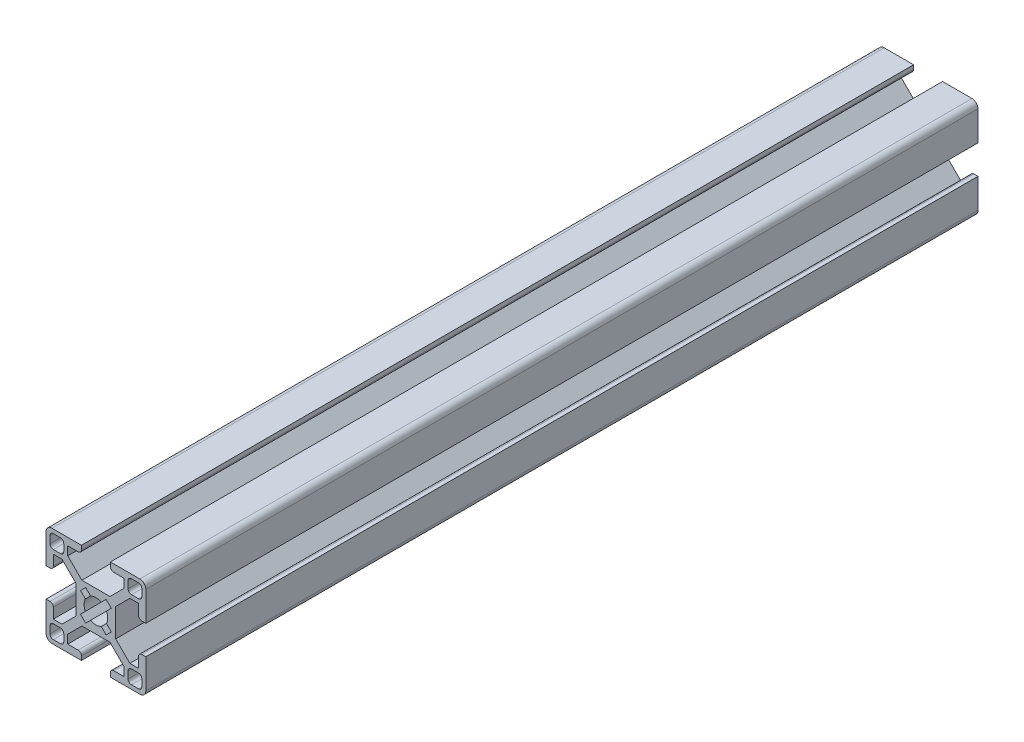
SolidWorks part; units mm, degrees
ref_plane "Front Plane" through (0, 0, 0) normal (0, 0, 1) x (1, 0, 0)
ref_plane "Top Plane" through (0, 0, 0) normal (0, 1, 0) x (1, 0, 0)
ref_plane "Right Plane" through (0, 0, 0) normal (1, 0, 0) x (0, 0, -1)
sketch "Sketch1" plane through (0, 0, 0) normal (0, 0, 1) x (1, 0, 0)
  line L0 (0, 0) -> (5.95, 0) construction
  line L1 (0, 0) -> (0, 5.95) construction
  line L2 (-5.95, 5.95) -> (5.95, 5.95)
  line L3 (5.95, 5.95) -> (5.95, 0)
  line L4 (4.2176, 5.95) -> (8.4602, 10.1926)
  line L5 (5.95, 5.95) -> (8.4425, 8.4425) construction
  line L6 (5.95, 4.2176) -> (10.1926, 8.4602)
  line L7 (8.4602, 12.7926) -> (8.4602, 8.4602)
  line L8 (8.4602, 8.4602) -> (12.7926, 8.4602)
  line L9 (12.7926, 8.4602) -> (12.7926, 5.3502)
  line L10 (13.7926, 4.3502) -> (14.9926, 4.3502)
  line L11 (14.9926, 4.3502) -> (14.9926, 13.1926)
  line L12 (8.4602, 8.4602) -> (14.9926, 14.9926) construction
  line L13 (4.3502, 13.7926) -> (4.3502, 14.9926)
  line L14 (4.3502, 14.9926) -> (13.1926, 14.9926)
  line L15 (5.3502, 12.7926) -> (8.4602, 12.7926)
  line L16 (-9.6602, 9.6602) -> (-13.7926, 13.7926) construction
  line L17 (10.6602, 13.7926) -> (12.7926, 13.7926)
  line L18 (9.6602, 12.7926) -> (9.6602, 10.6602)
  line L19 (10.6602, 9.6602) -> (12.7926, 9.6602)
  line L20 (13.7926, 12.7926) -> (13.7926, 10.6602)
  line L21 (9.6602, 13.7926) -> (13.7926, 9.6602) construction
  line L22 (9.6602, 9.6602) -> (13.7926, 13.7926) construction
  line L23 (-9.6602, 13.7926) -> (-13.7926, 9.6602) construction
  line L24 (-8.4602, 8.4602) -> (-14.9926, 14.9926) construction
  line L25 (-5.95, 5.95) -> (-8.4425, 8.4425) construction
  line L26 (-13.7926, 12.7926) -> (-13.7926, 10.6602)
  line L27 (-10.6602, 9.6602) -> (-12.7926, 9.6602)
  line L28 (-9.6602, 12.7926) -> (-9.6602, 10.6602)
  line L29 (-10.6602, 13.7926) -> (-12.7926, 13.7926)
  line L30 (-5.3502, 12.7926) -> (-8.4602, 12.7926)
  line L31 (-4.3502, 14.9926) -> (-13.1926, 14.9926)
  line L32 (-4.3502, 13.7926) -> (-4.3502, 14.9926)
  line L33 (-14.9926, 4.3502) -> (-14.9926, 13.1926)
  line L34 (-13.7926, 4.3502) -> (-14.9926, 4.3502)
  line L35 (-12.7926, 8.4602) -> (-12.7926, 5.3502)
  line L36 (-8.4602, 8.4602) -> (-12.7926, 8.4602)
  line L37 (-8.4602, 12.7926) -> (-8.4602, 8.4602)
  line L38 (-5.95, 4.2176) -> (-10.1926, 8.4602)
  line L39 (-4.2176, 5.95) -> (-8.4602, 10.1926)
  line L40 (-5.95, 5.95) -> (-5.95, 0)
  line L41 (-5.95, 0) -> (5.95, 0)
  arc A0 (13.1926, 14.9926) -> (14.9926, 13.1926) centre (13.1926, 13.1926) cw
  arc A1 (10.6602, 13.7926) -> (9.6602, 12.7926) centre (10.6602, 12.7926) ccw
  arc A2 (12.7926, 13.7926) -> (13.7926, 12.7926) centre (12.7926, 12.7926) cw
  arc A3 (12.7926, 9.6602) -> (13.7926, 10.6602) centre (12.7926, 10.6602) ccw
  arc A4 (9.6602, 10.6602) -> (10.6602, 9.6602) centre (10.6602, 10.6602) ccw
  arc A5 (4.3502, 13.7926) -> (5.3502, 12.7926) centre (5.3502, 13.7926) ccw
  arc A6 (12.7926, 5.3502) -> (13.7926, 4.3502) centre (13.7926, 5.3502) ccw
  arc A7 (-12.7926, 5.3502) -> (-13.7926, 4.3502) centre (-13.7926, 5.3502) cw
  arc A8 (-4.3502, 13.7926) -> (-5.3502, 12.7926) centre (-5.3502, 13.7926) cw
  arc A9 (-9.6602, 10.6602) -> (-10.6602, 9.6602) centre (-10.6602, 10.6602) cw
  arc A10 (-12.7926, 9.6602) -> (-13.7926, 10.6602) centre (-12.7926, 10.6602) cw
  arc A11 (-12.7926, 13.7926) -> (-13.7926, 12.7926) centre (-12.7926, 12.7926) ccw
  arc A12 (-10.6602, 13.7926) -> (-9.6602, 12.7926) centre (-10.6602, 12.7926) cw
  arc A13 (-13.1926, 14.9926) -> (-14.9926, 13.1926) centre (-13.1926, 13.1926) ccw
  point P12 (11.7264, 11.7264)
  point P40 (4.3502, 12.7926)
  point P43 (12.7926, 4.3502)
  point P82 (-12.7926, 4.3502)
  point P83 (-4.3502, 12.7926)
  point P84 (-11.7264, 11.7264)
  dimension "D9" = 1.8
  dimension "D10" = 1
  dimension "D11" = 1
  dimension "D1" = 5.95
  dimension "D4" = 2.6
  dimension "D2" = 135
  dimension "D3" = 2.45
  dimension "D5" = 6
  dimension "D6" = 4.11
  dimension "D7" = 2.2
  dimension "D8" = 1.2
extrude "Boss-Extrude1" add sketch "Sketch1" against normal blind 250 contours L31 A13 L33 L34 A7 L35 L36 L37 L30 A8 L32 L29 A12 L28 A9 L27 A10 L26 A11 | L40 L2 L39 L37 L36 L38 | L40 L41 L3 L2 | L8 L7 L4 L2 L3 L6 | L9 A6 L10 L11 A0 L14 L13 A5 L15 L7 L8 A4 L18 A1 L17 A2 L20 A3 L19
mirror "Mirror1" about plane through (0, 0, -250) normal (0, -1, 0) of bodies 101
sketch "Sketch2" plane through (0, 0, 0) normal (0, 0, 1) x (1, 0, 0)
  line L0 (-3.0759, -4.6315) -> (4.6315, 3.0759)
  line L1 (-3.0759, -4.6315) -> (-4.6315, -3.0759)
  line L2 (4.6315, 3.0759) -> (3.0759, 4.6315)
  line L3 (-4.6315, -3.0759) -> (3.0759, 4.6315)
  line L4 (-3.0759, -4.6315) -> (3.0759, 4.6315) construction
  line L5 (4.6315, 3.0759) -> (-4.6315, -3.0759) construction
  line L6 (0, 0) -> (0, 2.5254) construction
  line L7 (-4.6315, 3.0759) -> (3.0759, -4.6315)
  line L8 (-4.6315, 3.0759) -> (-3.0759, 4.6315)
  line L9 (-3.0759, 4.6315) -> (4.6315, -3.0759)
  line L10 (3.0759, -4.6315) -> (4.6315, -3.0759)
  line L11 (0, 0) -> (3.0759, 4.6315) construction
  line L12 (0, 0) -> (4.6315, -3.0759) construction
  circle A0 centre (0, 0) radius 3.555
  dimension "D1" = 7.11
  dimension "D2" = 45
  dimension "D3" = 2.2
  dimension "D4" = 10.9
  dimension "D6" = 90
  dimension "D5" = 2
extrude "Cut-Extrude1" cut sketch "Sketch2" against normal through all contours A0 L9 L8 L7 | L9 A0 L7 L3 | L7 A0 L3 | A0 L3 L1 L0 | L3 A0 L0 L7 | L0 A0 L7 | L7 A0 L9 L0 | L9 A0 L0 | L9 L3 L7 L0 | L0 A0 L3 L9 | L3 A0 L9 | A0 L0 L2 L3 | A0 L7 L10 L9
